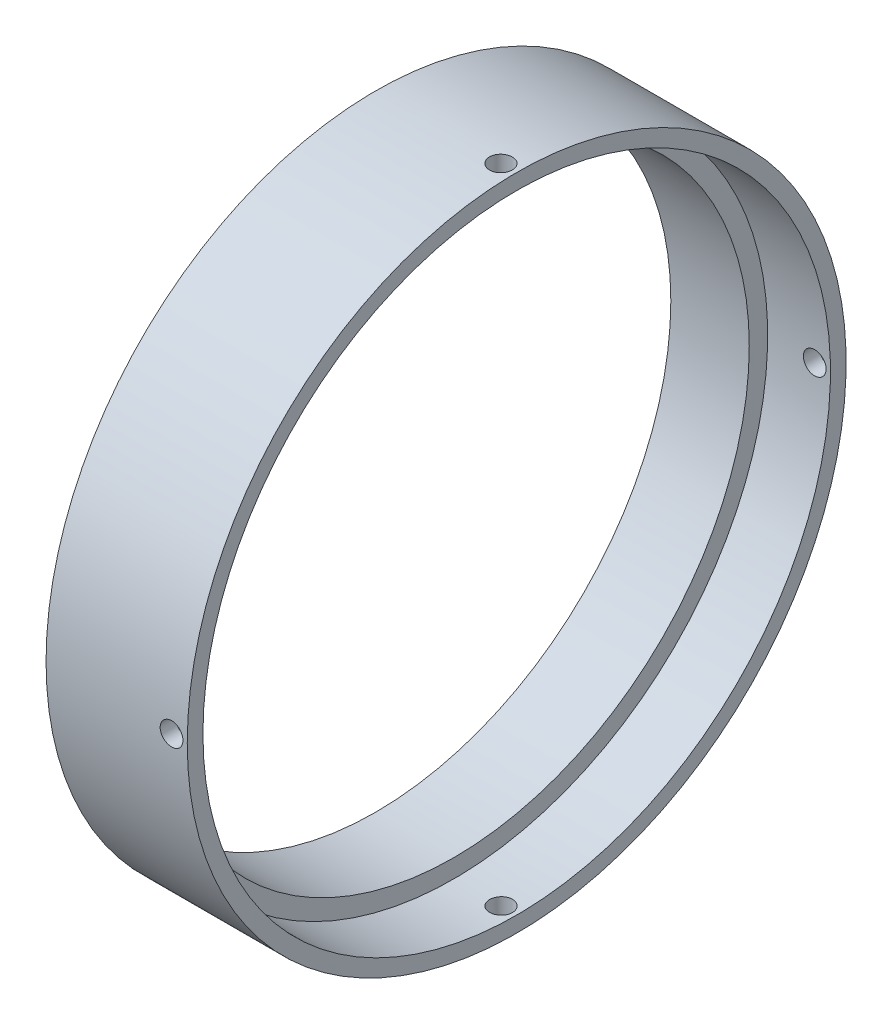
SolidWorks part; units mm, degrees
ref_plane "Plan de face" through (0, 0, 0) normal (0, 0, 1) x (1, 0, 0)
ref_plane "Plan de dessus" through (0, 0, 0) normal (0, 1, 0) x (1, 0, 0)
ref_plane "Plan de droite" through (0, 0, 0) normal (1, 0, 0) x (0, 0, -1)
sketch "Esquisse1" plane through (0, 0, 0) normal (0, 0, 1) x (1, 0, 0)
  line L0 (0, 42) -> (0, 37.65)
  line L1 (0, 37.65) -> (10, 37.65)
  line L2 (10, 37.65) -> (10, 40)
  line L3 (10, 40) -> (18, 40)
  line L4 (18, 40) -> (18, 42)
  line L5 (18, 42) -> (0, 42)
  line L6 (-19.4271, 0) -> (39.8195, 0) construction
  dimension "D1" = 10
  dimension "D2" = 8
  dimension "D3" = 37.65
  dimension "D4" = 42
  dimension "D5" = 40
revolve "Révolution1" add sketch "Esquisse1" angle 360 about L6
hole_wizard "Dégagement M2.51" positions "Esquisse3D1" profile "Esquisse2" hole size "M2.5" standard "ISO" end condition through all
sketch3d "Esquisse3D1"
  line L0 (9.575, 42, 0) -> (-6.7562, 42, 0) construction
  line L1 (-6.7562, 42, 0) -> (43.9232, 42, 0) construction
  line L3 (0, 0, 0) -> (0, 48.5877, 0) construction
  point P0 (16, 42, 0)
  point P11 (0, 0, 0)
  dimension "D1" = 16
sketch "Esquisse2" plane through (16, 42, 0) normal (1, 0, 0) x (0, 0, 1)
  line L0 (0, 0) -> (0, 84)
  line L1 (0, 84) -> (1.45, 84)
  line L2 (1.45, 84) -> (1.45, 0)
  line L5 (1.45, 0) -> (0, 0)
  line L11 (0, -6.35) -> (0, 107.95) construction
  dimension "Diamètre du perçage jusqu'au prochain" = 2.9
  dimension "Profondeur du perçage jusqu'au prochain" = 84
pattern_circular "Répétition circulaire1" count 2 over 90 about axis through (0, 0, 0) along (-1, 0, 0) of "Dégagement M2.51"
